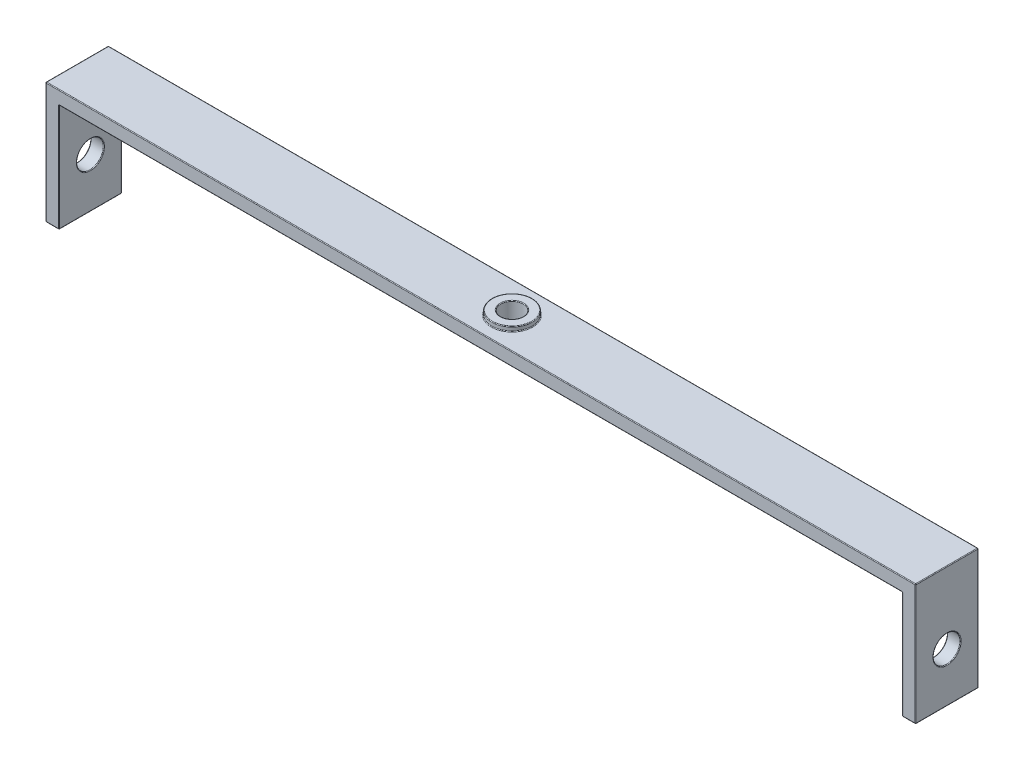
SolidWorks part; units mm, degrees
ref_plane "Front Plane" through (0, 0, 0) normal (0, 0, 1) x (1, 0, 0)
ref_plane "Top Plane" through (0, 0, 0) normal (0, 1, 0) x (1, 0, 0)
ref_plane "Right Plane" through (0, 0, 0) normal (1, 0, 0) x (0, 0, -1)
sketch "Sketch1" plane through (0, 0, 0) normal (0, 0, 1) x (1, 0, 0)
  line L0 (-47, 0) -> (47, 0)
  line L1 (47, 0) -> (47, -12)
  line L2 (-47, 0) -> (-47, -12)
  line L3 (-48.5, 1.5) -> (-48.5, -12)
  line L4 (-48.5, 1.5) -> (48.5, 1.5)
  line L5 (48.5, 1.5) -> (48.5, -12)
  line L6 (-48.5, -12) -> (-47, -12)
  line L7 (47, -12) -> (48.5, -12)
  dimension "D1" = 94
  dimension "D2" = 12
  dimension "D3" = 1.5
extrude "Boss-Extrude1" add sketch "Sketch1" along normal mid plane 7
sketch "Sketch2" plane through (0, 1.5, 0) normal (0, 1, 0) x (1, 0, 0)
  circle A0 centre (0, 0) radius 1.25
  dimension "D1" = 2.5
extrude "Cut-Extrude1" cut sketch "Sketch2" against normal up to surface (1.5 mm away) up to face at (0, 0, 0)
sketch "Sketch3" plane through (0, 1.5, 0) normal (0, 1, 0) x (1, 0, 0)
  circle A0 centre (0, 0) radius 1.25 construction
  circle A1 centre (0, 0) radius 1.25
  circle A2 centre (0, 0) radius 2.25
  dimension "D1" = 1
extrude "Boss-Extrude2" add sketch "Sketch3" along normal blind 0.5
sketch "Sketch4" plane through (0, 0, 0) normal (1, 0, 0) x (0, 0, -1)
  line L0 (0, 2) -> (0, -6.5) construction
  line L1 (1.25, 2) -> (-1.25, 2) construction
  circle A0 centre (0, -6.5) radius 1.5
  dimension "D2" = 3
  dimension "D1" = 8.5
extrude "Cut-Extrude2" cut sketch "Sketch4" against normal up to surface and the other way up to surface up to face at (-48.5, -5.25, 0) other way up to face at (48.5, -5.25, 0)
fillet "Fillet1" radius 0.075 32 edges at (48.5, -6.5, 1.5) (-48.5, -6.5, -1.5) (47, -5, 0) (-47, -8, 0) (0, 2, 1.25) (0, 2, 2.25) (0, 0, 1.25) (-47, -6, -3.5) (0, 0, -3.5) (47, -6, -3.5) (47.75, -12, -3.5) (48.5, -5.25, -3.5) (0, 1.5, -3.5) (-48.5, -5.25, -3.5) (-47.75, -12, -3.5) (-47, -6, 3.5) (0, 0, 3.5) (47, -6, 3.5) (47.75, -12, 3.5) (48.5, -5.25, 3.5) (-48.5, -5.25, 3.5) (-47.75, -12, 3.5) (-47, -12, 0) (-48.5, -12, 0) (-48.5, 1.5, 0) (48.5, 1.5, 0) (48.5, -12, 0) (47, -12, 0) (47, 0, 0) (-47, 0, 0) (0, 1.5, -2.25) (0, 1.5, 3.5)
